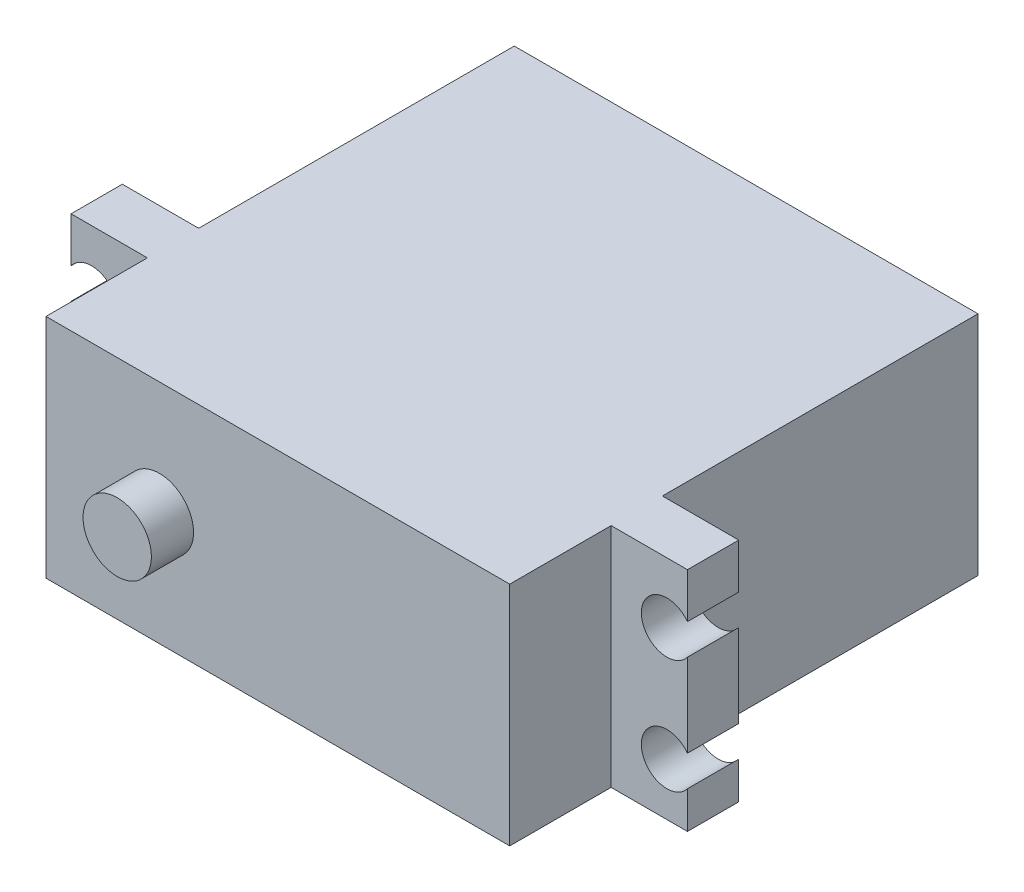
SolidWorks part; units mm, degrees
material "Custom Plastic"
ref_plane "Front Plane" through (0, 0, 0) normal (0, 0, 1) x (1, 0, 0)
ref_plane "Top Plane" through (0, 0, 0) normal (0, 1, 0) x (1, 0, 0)
ref_plane "Right Plane" through (0, 0, 0) normal (1, 0, 0) x (0, 0, -1)
sketch "Sketch1" plane through (0, 0, 0) normal (0, 0, 1) x (1, 0, 0)
  line L1 (-20.35, -9.95) -> (20.35, -9.95)
  line L2 (-20.35, -9.95) -> (-20.35, 9.95)
  line L3 (-20.35, 9.95) -> (20.35, 9.95)
  line L4 (20.35, -9.95) -> (20.35, 9.95)
  line L5 (-20.35, -9.95) -> (20.35, 9.95) construction
  line L6 (-20.35, 9.95) -> (20.35, -9.95) construction
  point P0 (0, 0)
  dimension "D1" = 19.9
  dimension "D2" = 40.7
extrude "Boss-Extrude1" add sketch "Sketch1" along normal blind 41.1
sketch "Sketch2" plane through (0, -9.95, 0) normal (0, -1, 0) x (1, 0, 0)
  line L0 (20.35, 41.1) -> (20.35, 0) construction
  line L1 (-27.05, 27.7) -> (27.05, 27.7)
  line L2 (-27.05, 27.7) -> (-27.05, 32.2)
  line L3 (-27.05, 32.2) -> (27.05, 32.2)
  line L4 (27.05, 27.7) -> (27.05, 32.2)
  line L5 (-20.35, 41.1) -> (-20.35, 0) construction
  dimension "D1" = 32.2
  dimension "D2" = 27.7
  dimension "D3" = 6.7
  dimension "D4" = 6.7
extrude "Boss-Extrude2" add sketch "Sketch2" against normal up to surface (19.9 mm away) up to face at (0, 9.95, 20.55)
sketch "Sketch3" plane through (0, 0, 32.2) normal (0, 0, 1) x (1, 0, 0)
  circle A0 centre (-25.25, 4.6498) radius 2.25
  circle A1 centre (-25.25, -5.3502) radius 2.25
  circle A2 centre (25.25, 4.6498) radius 2.25
  circle A3 centre (25.25, -5.3502) radius 2.25
  dimension "D6" = 4.5
  dimension "D7" = 4.5
  dimension "D8" = 4.5
  dimension "D9" = 4.5
  dimension "D1" = 50.5
  dimension "D2" = 50.5
  dimension "D3" = 10
  dimension "D4" = 10
  dimension "D5" = 25.25
extrude "Cut-Extrude1" cut sketch "Sketch3" against normal up to next
sketch "Sketch4" plane through (0, 0, 41.1) normal (0, 0, 1) x (1, 0, 0)
  circle A0 centre (-10.4, 0) radius 3
  dimension "D2" = 6
  dimension "D1" = 10.4
extrude "Boss-Extrude3" add sketch "Sketch4" along normal blind 3.7
sketch "Sketch6" plane through (-20.35, 0, 0) normal (-1, 0, 0) x (0, 0, 1)
  line L0 (0, 9.95) -> (0, -9.95) construction
  line L1 (8, 3.35) -> (3.5, 3.35)
  line L2 (8, 3.35) -> (8, -3.35)
  line L3 (8, -3.35) -> (3.5, -3.35)
  line L4 (3.5, 3.35) -> (3.5, -3.35)
  line L5 (27.7, -9.95) -> (0, -9.95) construction
  dimension "D1" = 3.5
  dimension "D2" = 6.7
  dimension "D3" = 6.6
  dimension "D4" = 8
extrude "Boss-Extrude4" add sketch "Sketch6" along normal blind 5.5 contours L3 L4 L1 L2
